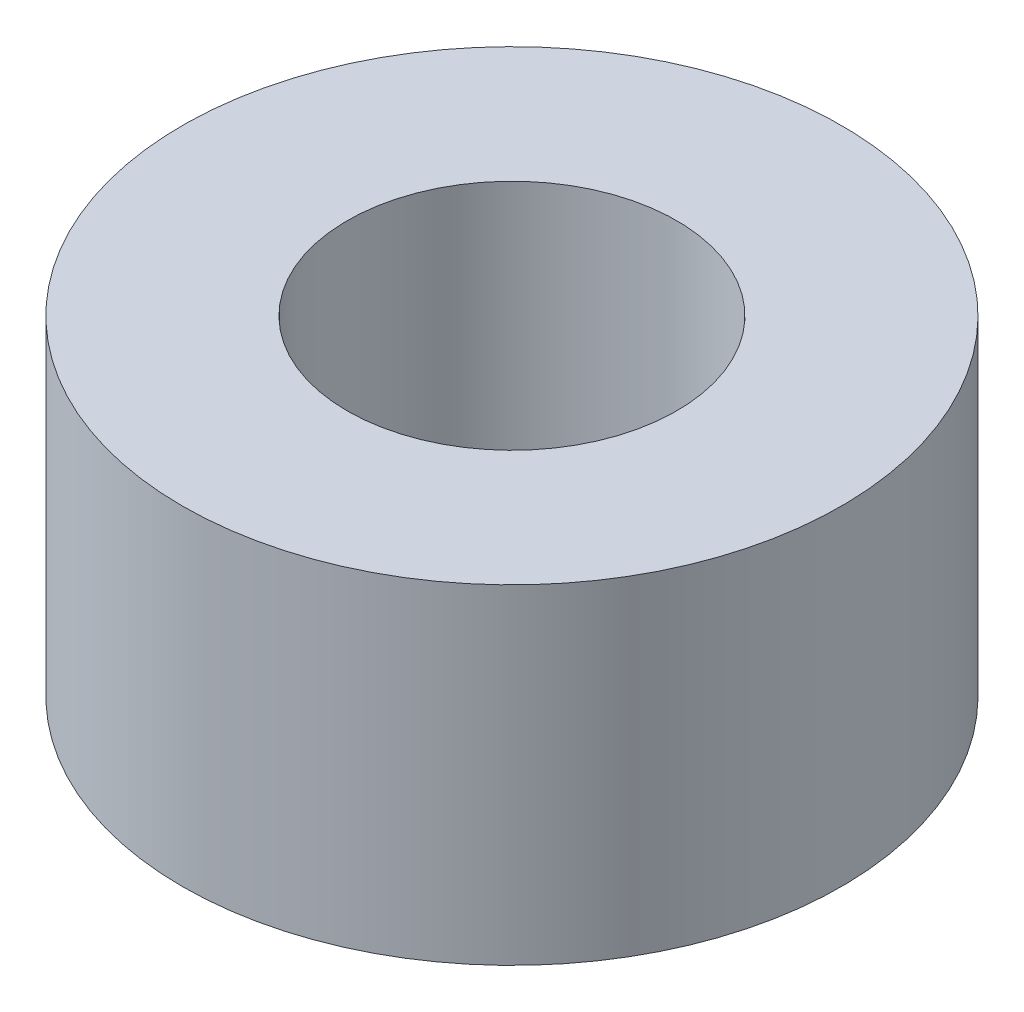
SolidWorks part; units mm, degrees
ref_plane "Front Plane" through (0, 0, 0) normal (0, 0, 1) x (1, 0, 0)
ref_plane "Top Plane" through (0, 0, 0) normal (0, 1, 0) x (1, 0, 0)
ref_plane "Right Plane" through (0, 0, 0) normal (1, 0, 0) x (0, 0, -1)
sketch "Sketch1" plane through (0, 0, 0) normal (0, 1, 0) x (1, 0, 0)
  circle A0 centre (0, 0) radius 3
  dimension "D1" = 6
extrude "Boss-Extrude1" add sketch "Sketch1" along normal blind 3
sketch "Sketch2" plane through (0, 3, 0) normal (0, 1, 0) x (1, 0, 0)
  circle A0 centre (0, 0) radius 1.5
  dimension "D1" = 3
extrude "Cut-Extrude1" cut sketch "Sketch2" against normal up to surface (3 mm away) up to face at (0, 0, 3)
